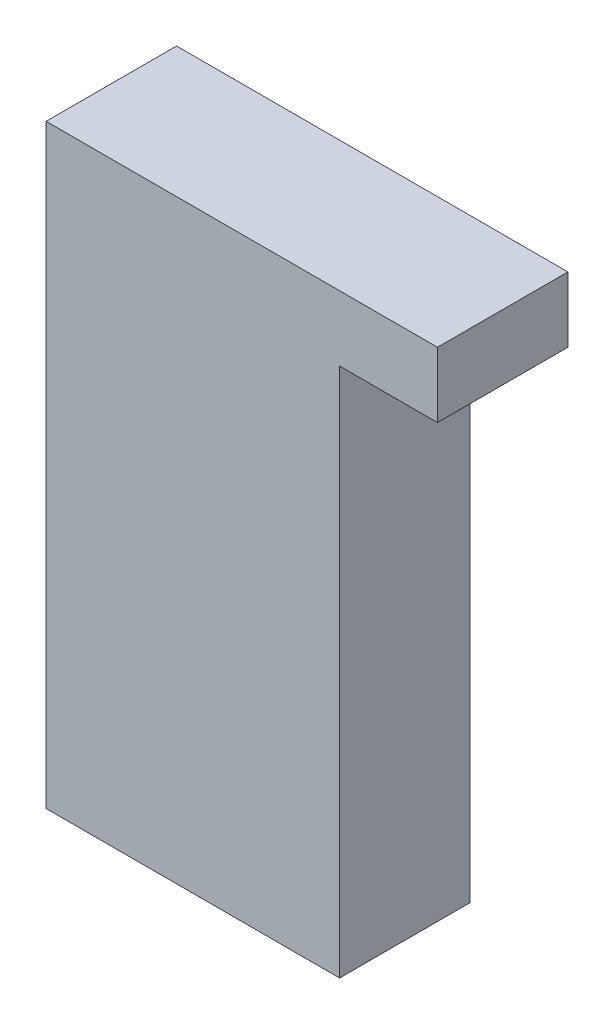
SolidWorks part; units mm, degrees
ref_plane "Front Plane" through (0, 0, 0) normal (0, 0, 1) x (1, 0, 0)
ref_plane "Top Plane" through (0, 0, 0) normal (0, 1, 0) x (1, 0, 0)
ref_plane "Right Plane" through (0, 0, 0) normal (1, 0, 0) x (0, 0, -1)
sketch "Sketch1" plane through (0, 0, 0) normal (0, 1, 0) x (1, 0, 0)
  line L1 (-18, 8) -> (18, 8)
  line L2 (-18, 8) -> (-18, -8)
  line L3 (-18, -8) -> (18, -8)
  line L4 (18, 8) -> (18, -8)
  line L5 (-18, 8) -> (18, -8) construction
  line L6 (-18, -8) -> (18, 8) construction
  point P0 (0, 0)
  dimension "D1" = 16
  dimension "D2" = 36
extrude "Boss-Extrude1" add sketch "Sketch1" along normal blind 73
sketch "Sketch2" plane through (18, 0, 0) normal (1, 0, 0) x (0, 0, -1)
  line L0 (8, 73) -> (8, 0) construction
  line L1 (-8, 73) -> (8, 73)
  line L2 (-8, 73) -> (-8, 65)
  line L3 (-8, 65) -> (8, 65)
  line L4 (8, 73) -> (8, 65)
  dimension "D1" = 8
extrude "Boss-Extrude2" add sketch "Sketch2" along normal blind 12
